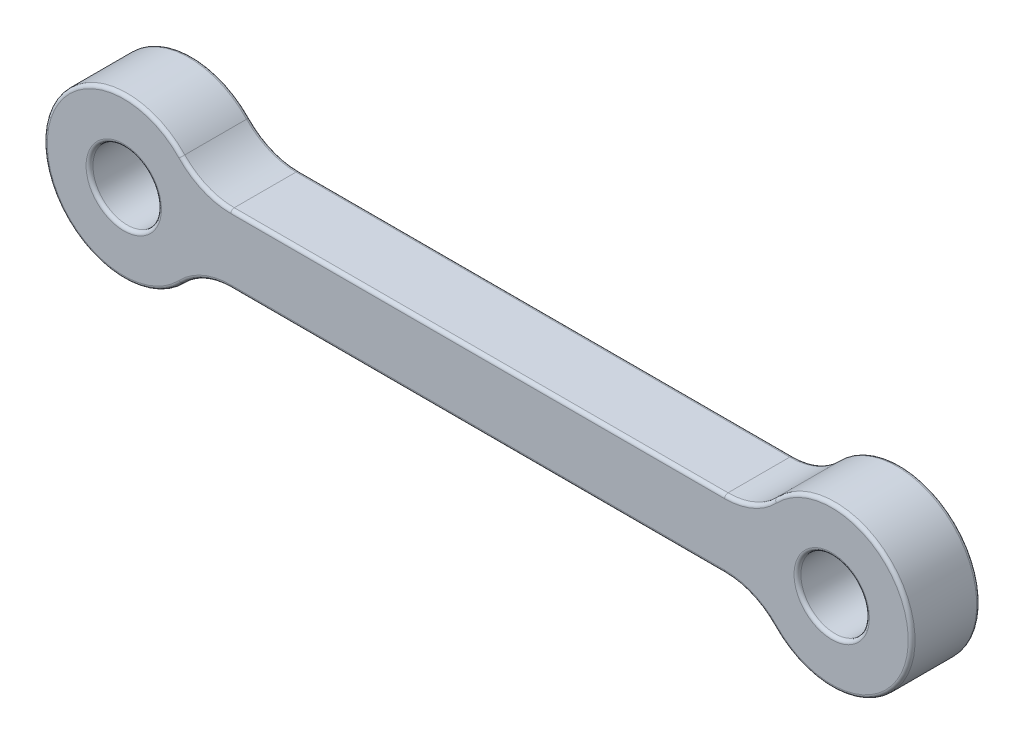
SolidWorks part; units mm, degrees
ref_plane "Front Plane" through (0, 0, 0) normal (0, 0, 1) x (1, 0, 0)
ref_plane "Top Plane" through (0, 0, 0) normal (0, 1, 0) x (1, 0, 0)
ref_plane "Right Plane" through (0, 0, 0) normal (1, 0, 0) x (0, 0, -1)
sketch "Sketch1" plane through (0, 0, 0) normal (0, 0, 1) x (1, 0, 0)
  line L0 (0, 0) -> (31, 0) construction
  line L1 (0, 3.5) -> (31, 3.5) construction
  line L2 (0, -3.5) -> (31, -3.5) construction
  line L3 (15.5, 0) -> (15.5, -3.5) construction
  line L5 (3.1623, -1.5) -> (27.8377, -1.5)
  line L6 (3.1623, -1.5) -> (3.1623, 1.5) construction
  line L7 (3.1623, 1.5) -> (27.8377, 1.5)
  line L8 (27.8377, -1.5) -> (27.8377, 1.5) construction
  line L9 (3.1623, -1.5) -> (27.8377, 1.5) construction
  line L10 (3.1623, 1.5) -> (27.8377, -1.5) construction
  arc A0 (0, 3.5) -> (0, -3.5) centre (0, 0) ccw construction
  arc A1 (31, -3.5) -> (31, 3.5) centre (31, 0) ccw construction
  circle A2 centre (0, 0) radius 3.5
  circle A3 centre (0, 0) radius 1.5
  circle A4 centre (31, 0) radius 1.5
  circle A5 centre (31, 0) radius 3.5
  point P3 (15.5, 0)
  dimension "D3" = 3
  dimension "D1" = 7
  dimension "D2" = 31
  dimension "D4" = 3
extrude "Boss-Extrude1" add sketch "Sketch1" along normal mid plane 3 contours A2 A3 | L5 A5 L7 A2 | A5 A4
fillet "Fillet1" radius 3 4 edges at (3.1623, -1.5, 0) (27.8377, -1.5, 0) (27.8377, 1.5, 0) (3.1623, 1.5, 0)
fillet "Fillet2" radius 0.15 20 edges at (32.5, 0, 1.5) (32.5, 0, -1.5) (1.5, 0, 1.5) (1.5, 0, -1.5) (3.5137, -1.7404, 1.5) (3.5137, -1.7404, -1.5) (15.5, -1.5, 1.5) (15.5, -1.5, -1.5) (27.4863, -1.7404, 1.5) (27.4863, -1.7404, -1.5) (34.5, 0, 1.5) (34.5, 0, -1.5) (27.4863, 1.7404, 1.5) (27.4863, 1.7404, -1.5) (15.5, 1.5, 1.5) (15.5, 1.5, -1.5) (3.5137, 1.7404, 1.5) (3.5137, 1.7404, -1.5) (-3.5, 0, -1.5) (-3.5, 0, 1.5)
